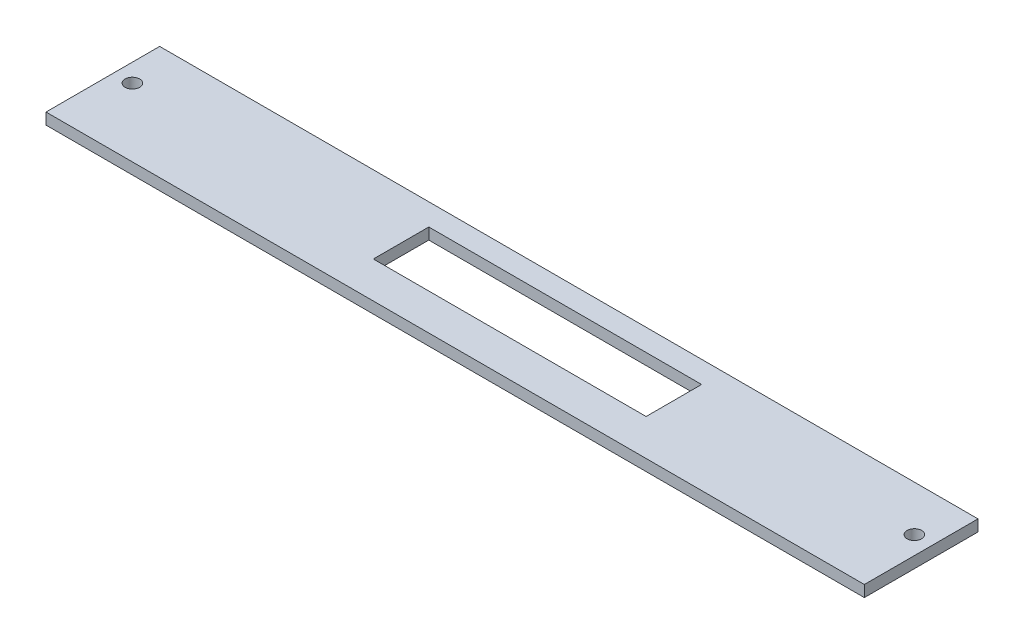
SolidWorks part; units mm, degrees
ref_plane "Front Plane" through (0, 0, 0) normal (0, 0, 1) x (1, 0, 0)
ref_plane "Top Plane" through (0, 0, 0) normal (0, 1, 0) x (1, 0, 0)
ref_plane "Right Plane" through (0, 0, 0) normal (1, 0, 0) x (0, 0, -1)
sketch "Sketch1" plane through (0, 0, 0) normal (0, 1, 0) x (1, 0, 0)
  line L1 (0, 0) -> (228.6, 0)
  line L2 (0, 0) -> (0, 31.75)
  line L3 (0, 31.75) -> (228.6, 31.75)
  line L4 (228.6, 0) -> (228.6, 31.75)
  dimension "D1" = 31.75
  dimension "D2" = 228.6
extrude "Boss-Extrude1" add sketch "Sketch1" along normal blind 3.175
sketch "Sketch2" plane through (0, 3.175, 0) normal (0, 1, 0) x (1, 0, 0)
  line L1 (0, 31.75) -> (0, 0) construction
  line L2 (228.6, 0) -> (228.6, 31.75) construction
  line L3 (228.6, 31.75) -> (0, 31.75) construction
  circle A0 centre (5.08, 19.05) radius 2.032
  circle A1 centre (223.52, 19.05) radius 2.032
  point P4 (0, 0)
  point P5 (0, 0)
  point P8 (0, 0)
  dimension "D1" = 4.064
  dimension "D2" = 12.7
  dimension "D3" = 5.08
  dimension "D4" = 5.08
extrude "Cut-Extrude1" cut sketch "Sketch2" against normal blind 3.175
sketch "Sketch3" plane through (0, 3.175, 0) normal (0, 1, 0) x (1, 0, 0)
  line L0 (0, 0) -> (228.6, 0) construction
  line L1 (81.28, 25.654) -> (157.48, 25.654)
  line L2 (81.28, 25.654) -> (81.28, 10.16)
  line L3 (81.28, 10.16) -> (157.48, 10.16)
  line L4 (157.48, 25.654) -> (157.48, 10.16)
  line L5 (228.6, 31.75) -> (0, 31.75) construction
  line L6 (0, 31.75) -> (0, 0) construction
  dimension "D1" = 76.2
  dimension "D2" = 10.16
  dimension "D3" = 6.096
  dimension "D4" = 81.28
extrude "Cut-Extrude2" cut sketch "Sketch3" against normal blind 3.175
